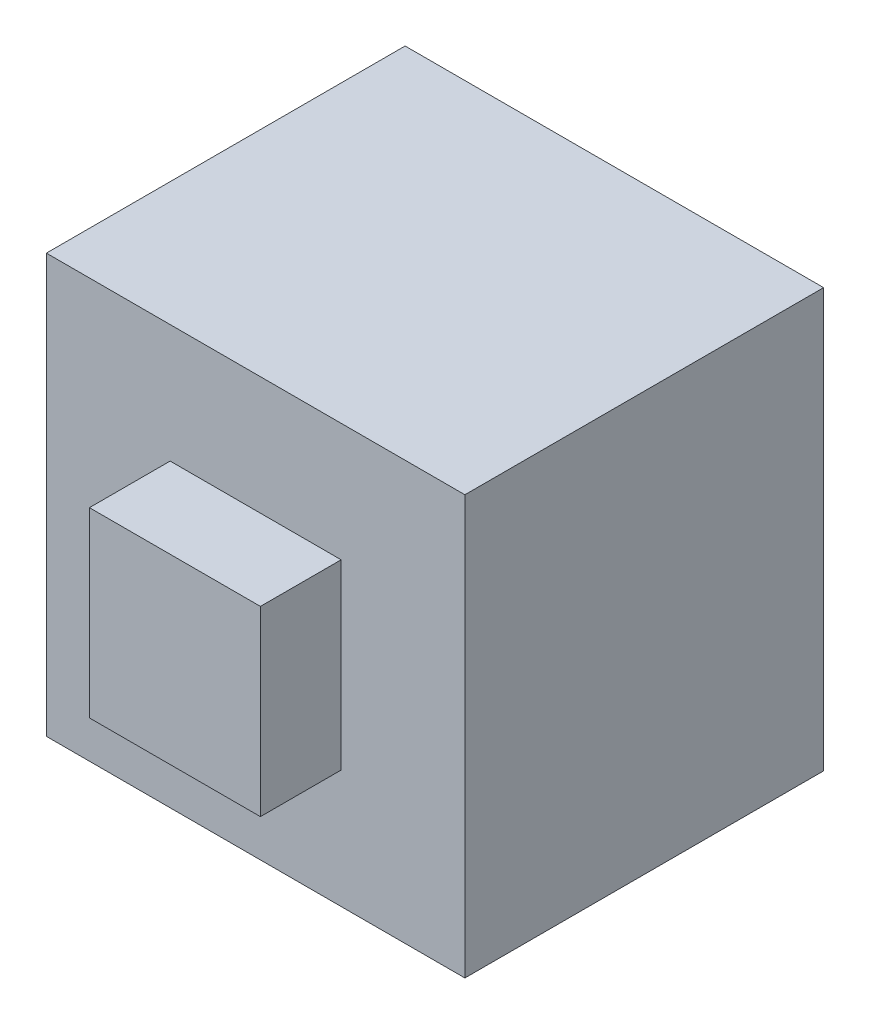
SolidWorks part; units mm, degrees
ref_plane "Front Plane" through (0, 0, 0) normal (0, 0, 1) x (1, 0, 0)
ref_plane "Top Plane" through (0, 0, 0) normal (0, 1, 0) x (1, 0, 0)
ref_plane "Right Plane" through (0, 0, 0) normal (1, 0, 0) x (0, 0, -1)
sketch "Sketch2" plane through (0, 0, 0) normal (0, 0, 1) x (1, 0, 0)
  line L1 (-70, 70) -> (70, 70)
  line L2 (-70, 70) -> (-70, -70)
  line L3 (-70, -70) -> (70, -70)
  line L4 (70, 70) -> (70, -70)
  line L5 (-70, 70) -> (70, -70) construction
  line L6 (-70, -70) -> (70, 70) construction
  point P0 (0, 0)
  dimension "D1" = 140
  dimension "D2" = 140
extrude "Boss-Extrude1" add sketch "Sketch2" along normal blind 120
sketch "Sketch3" plane through (0, 0, 120) normal (0, 0, 1) x (1, 0, 0)
  line L1 (-28.5996, 30.4567) -> (28.5996, 30.4567)
  line L2 (-28.5996, 30.4567) -> (-28.5996, -30.4567)
  line L3 (-28.5996, -30.4567) -> (28.5996, -30.4567)
  line L4 (28.5996, 30.4567) -> (28.5996, -30.4567)
  line L5 (-28.5996, 30.4567) -> (28.5996, -30.4567) construction
  line L6 (-28.5996, -30.4567) -> (28.5996, 30.4567) construction
  point P0 (0, 0)
extrude "Boss-Extrude2" add sketch "Sketch3" along normal blind 27
